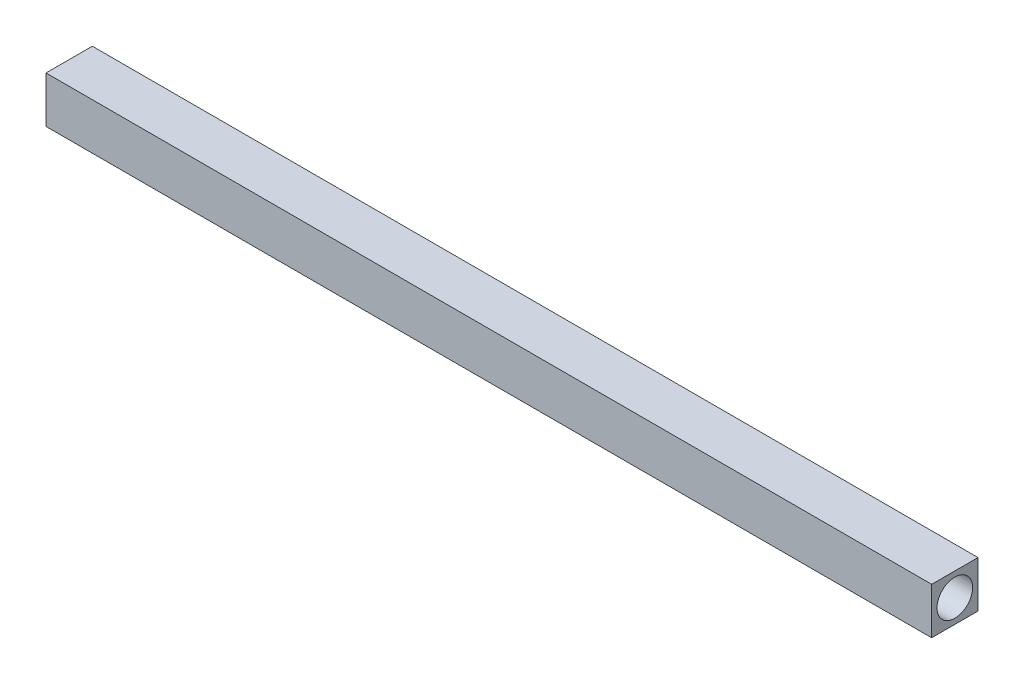
SolidWorks part; units mm, degrees
ref_plane "Front Plane" through (0, 0, 0) normal (0, 0, 1) x (1, 0, 0)
ref_plane "Top Plane" through (0, 0, 0) normal (0, 1, 0) x (1, 0, 0)
ref_plane "Right Plane" through (0, 0, 0) normal (1, 0, 0) x (0, 0, -1)
sketch "Sketch1" plane through (0, 0, 0) normal (1, 0, 0) x (0, 0, -1)
  line L1 (-1.651, 1.651) -> (1.651, 1.651)
  line L2 (-1.651, 1.651) -> (-1.651, -1.651)
  line L3 (-1.651, -1.651) -> (1.651, -1.651)
  line L4 (1.651, 1.651) -> (1.651, -1.651)
  line L5 (-1.651, 1.651) -> (1.651, -1.651) construction
  line L6 (-1.651, -1.651) -> (1.651, 1.651) construction
  point P0 (0, 0)
  dimension "D1" = 3.302
extrude "Boss-Extrude1" add sketch "Sketch1" along normal mid plane 63.119
sketch "Sketch2" plane through (31.5595, 0, 0) normal (1, 0, 0) x (0, 0, -1)
  circle A0 centre (0, 0) radius 1.27
  dimension "D1" = 2.54
extrude "Cut-Extrude1" cut sketch "Sketch2" against normal blind 3.175
mirror "Mirror1" about plane through (0, 0, 0) normal (1, 0, 0) of "Cut-Extrude1"
